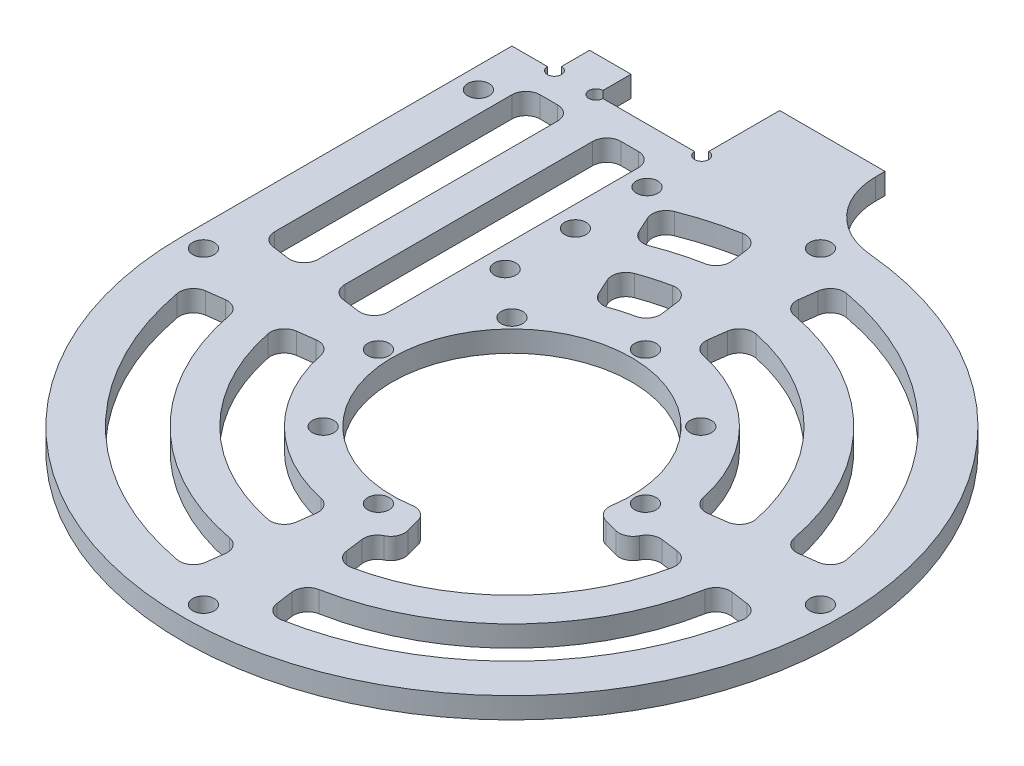
SolidWorks part; units mm, degrees
material "Thornel Mat VMA"
ref_plane "前视基准面" through (0, 0, 0) normal (0, 0, 1) x (1, 0, 0)
ref_plane "上视基准面" through (0, 0, 0) normal (0, 1, 0) x (1, 0, 0)
ref_plane "右视基准面" through (0, 0, 0) normal (1, 0, 0) x (0, 0, -1)
sketch "草图1" plane through (0, 0, 0) normal (0, 1, 0) x (1, 0, 0)
  line L0 (-46.9, 0) -> (-46.9, 46.9)
  line L1 (-46.9, 46.9) -> (-16.9, 46.9)
  line L2 (-16.9, 46.9) -> (-16.9, 46.5747)
  line L3 (-31.9, 0) -> (-31.9, 46.9) construction
  line L4 (-19.9, 46.9) -> (-19.9, 39.1306) construction
  line L5 (-19.9, 46.9) -> (-19.9, 43.7493) construction
  line L6 (-43.9, 0) -> (-43.9, 46.9) construction
  line L7 (-16.9, 46.9) -> (-16.9, 43.7493) construction
  line L8 (-22.9, 0) -> (-22.9, 46.9) construction
  line L9 (-19.9, 39.1306) -> (-19.9, 18.9319) construction
  arc A0 (-46.9, 0) -> (-14.2906, 44.6698) centre (0, 0) ccw
  circle A1 centre (0, 0) radius 40.9 construction
  circle A2 centre (0, 0) radius 31.9 construction
  circle A3 centre (0, 0) radius 22.9 construction
  circle A4 centre (0, 0) radius 43.9 construction
  circle A5 centre (-19.9, 39.1306) radius 1.525
  circle A6 centre (0, 43.9) radius 1.525
  circle A7 centre (43.9, 0) radius 1.525
  circle A8 centre (0, -43.9) radius 1.525
  circle A9 centre (-43.9, 0) radius 1.525
  circle A10 centre (0, 0) radius 17.025
  circle A11 centre (0, 0) radius 19 construction
  circle A12 centre (0, 19) radius 1.525
  circle A13 centre (13.435, 13.435) radius 1.525
  circle A14 centre (19, 0) radius 1.525
  circle A15 centre (13.435, -13.435) radius 1.525
  circle A16 centre (0, -19) radius 1.525
  circle A17 centre (-13.435, -13.435) radius 1.525
  circle A18 centre (-19, 0) radius 1.525
  circle A19 centre (-13.435, 13.435) radius 1.525
  circle A20 centre (0, 0) radius 46.9 construction
  circle A21 centre (-43.9, 39.1306) radius 1.525
  arc A22 (-16.9, 46.5747) -> (-14.2906, 44.6698) centre (-14.9, 46.5747) ccw
  circle A23 centre (-19.9, 28.9319) radius 1.525
  circle A24 centre (-19.9, 18.9319) radius 1.525
  circle A25 centre (39.0795, -20) radius 1.525 construction
  point P58 (-19.9, 24.9319)
  dimension "D1" = 93.8
  dimension "D8" = 3.05
  dimension "D9" = 34.05
  dimension "D10" = 38
  dimension "D11" = 3.05
  dimension "D13" = 2
  dimension "D14" = 4
  dimension "D16" = 20
  dimension "D15" = 6
  dimension "D2" = 6
  dimension "D3" = 9
  dimension "D4" = 9
  dimension "D5" = 3
  dimension "D6" = 3
  dimension "D7" = 4
  dimension "D12" = 8
extrude "凸台-拉伸1" add sketch "草图1" along normal blind 3
sketch "草图2" plane through (0, 0, 0) normal (0, 1, 0) x (1, 0, 0)
  line L0 (-40.9, 7.1385) -> (-40.9, 40.9)
  line L1 (-38.9, 42.9) -> (-36.4, 42.9)
  line L2 (-22.9, 0) -> (-22.9, 46.9) construction
  line L3 (-22.9, 40.9) -> (-22.9, 5.2954)
  line L4 (-29.4, 0) -> (-29.4, 46.9)
  line L5 (-29.4, 5.6245) -> (-29.4, 40.9)
  line L6 (-34.4, 0) -> (-34.4, 46.9)
  line L7 (-34.4, 6.8094) -> (-34.4, 40.9)
  line L8 (-46.9, 46.9) -> (-16.9, 46.9) construction
  line L9 (-27.4, 42.9) -> (-24.9, 42.9)
  line L10 (-16.0523, 35.377) -> (-15.0179, 33.0972)
  line L11 (-3.5669, 27.0931) -> (-3.2396, 24.6072)
  line L12 (0, 0) -> (-43.9, 0) construction
  line L13 (0, 0) -> (0, -43.9) construction
  line L14 (0, 0) -> (43.9, 0) construction
  line L15 (0, 0) -> (0, 29.4) construction
  line L16 (-5.0708, 38.5162) -> (-4.744, 36.0341)
  line L17 (5.0708, 38.5162) -> (4.744, 36.0341)
  line L18 (-11.2916, 24.8849) -> (-10.2555, 22.6016)
  line L19 (0, 34.4) -> (0, 43.9) construction
  line L20 (3.5669, 27.0931) -> (3.2396, 24.6072)
  line L21 (38.5162, 5.0708) -> (36.0341, 4.744)
  line L22 (27.0931, 3.5669) -> (24.6072, 3.2396)
  line L23 (38.5162, -5.0708) -> (36.0341, -4.744)
  line L24 (27.0931, -3.5669) -> (24.6072, -3.2396)
  line L25 (5.0708, -38.5162) -> (4.744, -36.0341)
  line L26 (3.5669, -27.0931) -> (3.2396, -24.6072)
  line L27 (-5.0708, -38.5162) -> (-4.744, -36.0341)
  line L28 (-3.5669, -27.0931) -> (-3.2396, -24.6072)
  line L29 (-38.5162, -5.0708) -> (-36.0341, -4.744)
  line L30 (-27.0931, -3.5669) -> (-24.6072, -3.2396)
  line L31 (-39.1611, 5.1557) -> (-36.6611, 4.8265)
  line L32 (-27.6611, 3.6416) -> (-25.1611, 3.3125)
  circle A0 centre (0, 0) radius 22.9 construction
  circle A1 centre (0, 0) radius 40.9 construction
  arc A2 (-22.3906, -4.803) -> (-4.803, -22.3906) centre (0, 0) ccw
  circle A3 centre (0, 0) radius 34.4
  arc A4 (-33.8075, -6.3573) -> (-6.3573, -33.8075) centre (0, 0) ccw
  circle A5 centre (0, 0) radius 29.4
  arc A6 (-28.7906, -5.9549) -> (-5.9549, -28.7906) centre (0, 0) ccw
  arc A7 (-40.222, -7.4163) -> (-7.4163, -40.222) centre (0, 0) ccw
  arc A8 (-7.4163, 40.222) -> (-14.9627, 38.0648) centre (0, 0) ccw
  arc A9 (-6.3573, 33.8075) -> (-12.4715, 32.0597) centre (0, 0) ccw
  arc A10 (-5.9549, 28.7906) -> (-10.1615, 27.5881) centre (0, 0) ccw
  arc A11 (-4.803, 22.3906) -> (-7.7568, 21.5463) centre (0, 0) ccw
  arc A12 (40.222, 7.4163) -> (7.4163, 40.222) centre (0, 0) ccw
  arc A13 (33.8075, 6.3573) -> (6.3573, 33.8075) centre (0, 0) ccw
  arc A14 (28.7906, 5.9549) -> (5.9549, 28.7906) centre (0, 0) ccw
  arc A15 (22.3906, 4.803) -> (4.803, 22.3906) centre (0, 0) ccw
  arc A16 (7.4163, -40.222) -> (40.222, -7.4163) centre (0, 0) ccw
  arc A17 (6.3573, -33.8075) -> (33.8075, -6.3573) centre (0, 0) ccw
  arc A18 (5.9549, -28.7906) -> (28.7906, -5.9549) centre (0, 0) ccw
  arc A19 (4.803, -22.3906) -> (22.3906, -4.803) centre (0, 0) ccw
  arc A20 (-39.1611, 5.1557) -> (-40.9, 7.1385) centre (-38.9, 7.1385) cw
  arc A21 (-36.6611, 4.8265) -> (-34.4, 6.8094) centre (-36.4, 6.8094) ccw
  arc A22 (-27.6611, 3.6416) -> (-29.4, 5.6245) centre (-27.4, 5.6245) cw
  arc A23 (-25.1611, 3.3125) -> (-22.9, 5.2954) centre (-24.9, 5.2954) ccw
  arc A24 (-22.9, 40.9) -> (-24.9, 42.9) centre (-24.9, 40.9) ccw
  arc A25 (-29.4, 40.9) -> (-27.4, 42.9) centre (-27.4, 40.9) cw
  arc A26 (-34.4, 40.9) -> (-36.4, 42.9) centre (-36.4, 40.9) ccw
  arc A27 (-40.9, 40.9) -> (-38.9, 42.9) centre (-38.9, 40.9) cw
  arc A28 (5.0708, -38.5162) -> (7.4163, -40.222) centre (7.0536, -38.2551) ccw
  arc A29 (3.5669, -27.0931) -> (5.9549, -28.7906) centre (5.5498, -26.8321) ccw
  arc A30 (3.2396, -24.6072) -> (4.803, -22.3906) centre (5.2225, -24.3462) cw
  arc A31 (4.744, -36.0341) -> (6.3573, -33.8075) centre (6.7269, -35.773) cw
  arc A32 (-5.0708, -38.5162) -> (-7.4163, -40.222) centre (-7.0536, -38.2551) cw
  arc A33 (-4.744, -36.0341) -> (-6.3573, -33.8075) centre (-6.7269, -35.773) ccw
  arc A34 (-3.5669, -27.0931) -> (-5.9549, -28.7906) centre (-5.5498, -26.8321) cw
  arc A35 (-3.2396, -24.6072) -> (-4.803, -22.3906) centre (-5.2225, -24.3462) ccw
  arc A36 (-24.6072, -3.2396) -> (-22.3906, -4.803) centre (-24.3462, -5.2225) cw
  arc A37 (-27.0931, -3.5669) -> (-28.7906, -5.9549) centre (-26.8321, -5.5498) ccw
  arc A38 (-36.0341, -4.744) -> (-33.8075, -6.3573) centre (-35.773, -6.7269) cw
  arc A39 (-38.5162, -5.0708) -> (-40.222, -7.4163) centre (-38.2551, -7.0536) ccw
  arc A40 (-4.803, 22.3906) -> (-3.2396, 24.6072) centre (-5.2225, 24.3462) ccw
  arc A41 (-3.5669, 27.0931) -> (-5.9549, 28.7906) centre (-5.5498, 26.8321) ccw
  arc A42 (-4.744, 36.0341) -> (-6.3573, 33.8075) centre (-6.7269, 35.773) cw
  arc A43 (-5.0708, 38.5162) -> (-7.4163, 40.222) centre (-7.0536, 38.2551) ccw
  arc A44 (-12.4715, 32.0597) -> (-15.0179, 33.0972) centre (-13.1966, 33.9236) cw
  arc A45 (-16.0523, 35.377) -> (-14.9627, 38.0648) centre (-14.2311, 36.2034) cw
  arc A46 (-10.1615, 27.5881) -> (-11.2916, 24.8849) centre (-9.4703, 25.7114) ccw
  arc A47 (-10.2555, 22.6016) -> (-7.7568, 21.5463) centre (-8.4342, 23.4281) ccw
  arc A48 (38.5162, 5.0708) -> (40.222, 7.4163) centre (38.2551, 7.0536) ccw
  arc A49 (36.0341, 4.744) -> (33.8075, 6.3573) centre (35.773, 6.7269) cw
  arc A50 (27.0931, 3.5669) -> (28.7906, 5.9549) centre (26.8321, 5.5498) ccw
  arc A51 (24.6072, 3.2396) -> (22.3906, 4.803) centre (24.3462, 5.2225) cw
  arc A52 (4.803, 22.3906) -> (3.2396, 24.6072) centre (5.2225, 24.3462) cw
  arc A53 (3.5669, 27.0931) -> (5.9549, 28.7906) centre (5.5498, 26.8321) cw
  arc A54 (4.744, 36.0341) -> (6.3573, 33.8075) centre (6.7269, 35.773) ccw
  arc A55 (5.0708, 38.5162) -> (7.4163, 40.222) centre (7.0536, 38.2551) cw
  arc A56 (27.0931, -3.5669) -> (28.7906, -5.9549) centre (26.8321, -5.5498) cw
  arc A57 (36.0341, -4.744) -> (33.8075, -6.3573) centre (35.773, -6.7269) ccw
  arc A58 (38.5162, -5.0708) -> (40.222, -7.4163) centre (38.2551, -7.0536) cw
  arc A59 (24.6072, -3.2396) -> (22.3906, -4.803) centre (24.3462, -5.2225) ccw
  point P81 (-22.9, 42.9)
  point P84 (-29.4, 42.9)
  point P115 (-2.989, 22.7041)
  point P118 (-3.8375, 29.1485)
  point P121 (-4.4901, 34.1057)
  point P124 (-5.3385, 40.5501)
  point P129 (-16.9, 37.2451)
  point P132 (-12.1482, 26.7728)
  point P143 (22.7041, 2.989)
  point P146 (2.989, 22.7041)
  point P153 (5.3385, 40.5501)
  dimension "D8" = 2
  dimension "D9" = 2
  dimension "D10" = 2
  dimension "D11" = 2
  dimension "D12" = 2
  dimension "D5" = 4
  dimension "D6" = 15
  dimension "D1" = 2.5
  dimension "D2" = 2.5
  dimension "D3" = 2.5
  dimension "D4" = 2.5
  dimension "D7" = 4
extrude "切除-拉伸2" cut sketch "草图2" along normal through all
sketch "草图3" plane through (0, 3, 0) normal (0, 1, 0) x (1, 0, 0)
  line L0 (0, 0) -> (13.435, -13.435) construction
  line L1 (0, 0) -> (5.927, -22.1197)
  line L2 (0, 0) -> (22.1197, -5.927)
  arc A0 (4.803, -22.3906) -> (22.3906, -4.803) centre (0, 0) ccw construction
  arc A1 (5.927, -22.1197) -> (22.1197, -5.927) centre (0, 0) ccw
  dimension "D1" = 30
extrude "切除-拉伸3" cut sketch "草图3" against normal through all
fillet "圆角1" radius 2 4 edges at (5.927, 1.5, 22.1197) (4.4064, 1.5, 16.4449) (16.4449, 1.5, 4.4064) (22.1197, 1.5, 5.927)
sketch "草图5" plane through (0, 0, 0) normal (0, 1, 0) x (1, 0, 0)
  line L5 (-16.9, 46.9) -> (-46.9, 46.9) construction
  line L6 (-16.9, 46.9) -> (-16.9, 51.9) construction
  line L7 (-16.9, 51.9) -> (-46.9, 51.9) construction
  line L8 (-46.9, 46.9) -> (-46.9, 51.9) construction
  line L9 (-46.9, 46.9) -> (-46.9, 0) construction
  line L10 (-16.9, 46.9) -> (-16.9, 51.9) construction
  line L11 (-16.9, 51.9) -> (-19.9, 51.9) construction
  line L13 (-19.9, 46.9) -> (-16.9, 46.9) construction
  line L14 (-46.9, 46.9) -> (-46.9, 51.9) construction
  line L15 (-46.9, 51.9) -> (-44.9, 51.9) construction
  line L16 (-44.9, 51.9) -> (-44.9, 46.9) construction
  line L17 (-44.9, 46.9) -> (-46.9, 46.9) construction
  line L18 (-31.9, 46.9) -> (-31.9, 51.9) construction
  line L19 (-40.85, 51.9) -> (-34.95, 51.9)
  line L20 (-22.95, 46.9) -> (-28.85, 46.9) construction
  line L21 (-22.95, 46.9) -> (-22.95, 51.9) construction
  line L22 (-22.95, 51.9) -> (-28.85, 51.9) construction
  line L23 (-28.85, 46.9) -> (-28.85, 51.9) construction
  line L24 (-34.95, 46.9) -> (-34.95, 51.9) construction
  line L25 (-40.85, 46.9) -> (-34.95, 46.9)
  line L26 (-40.85, 46.9) -> (-40.85, 51.9)
  line L27 (-34.95, 46.9) -> (-28.85, 46.9) construction
  line L28 (-4.9, 43.9) -> (-19.9, 43.9)
  line L29 (-4.9, 43.9) -> (-4.9, 58)
  line L30 (-4.9, 58) -> (-19.9, 58)
  line L31 (-19.9, 43.9) -> (-19.9, 46.9)
  line L32 (-28.85, 51.9) -> (-34.95, 51.9) construction
  line L34 (-19.9, 51.9) -> (-19.9, 58)
  line L35 (-19.9, 51.9) -> (-19.9, 46.9)
  line L36 (-28.85, 46.9) -> (-22.95, 46.9) construction
  line L38 (-22.95, 51.9) -> (-28.85, 51.9) construction
  line L39 (-22.95, 46.9) -> (-22.95, 51.9) construction
  line L40 (-34.95, 46.9) -> (-34.95, 51.9)
  dimension "D2" = 17.9
  dimension "D3" = 6.1
  dimension "D4" = 5
  dimension "D5" = 3
  dimension "D6" = 11.1
  dimension "D7" = 15
  dimension "D8" = 3.05
extrude "凸台-拉伸3" add sketch "草图5" along normal up to surface (3 mm away) up to face at (12.1553, 3, 12.1553)
fillet "圆角3" radius 10 1 edges at (-4.9, 1.5, -46.6433)
sketch "草图6" plane through (0, 0, 0) normal (0, 1, 0) x (1, 0, 0)
  circle A0 centre (-22.95, 46.9) radius 1 construction
  circle A1 centre (-19.9, 46.9) radius 1
  circle A2 centre (-40.85, 46.9) radius 1
  circle A4 centre (-34.95, 46.9) radius 1
  dimension "D1" = 2
extrude "切除-拉伸7" cut sketch "草图6" along normal through all
